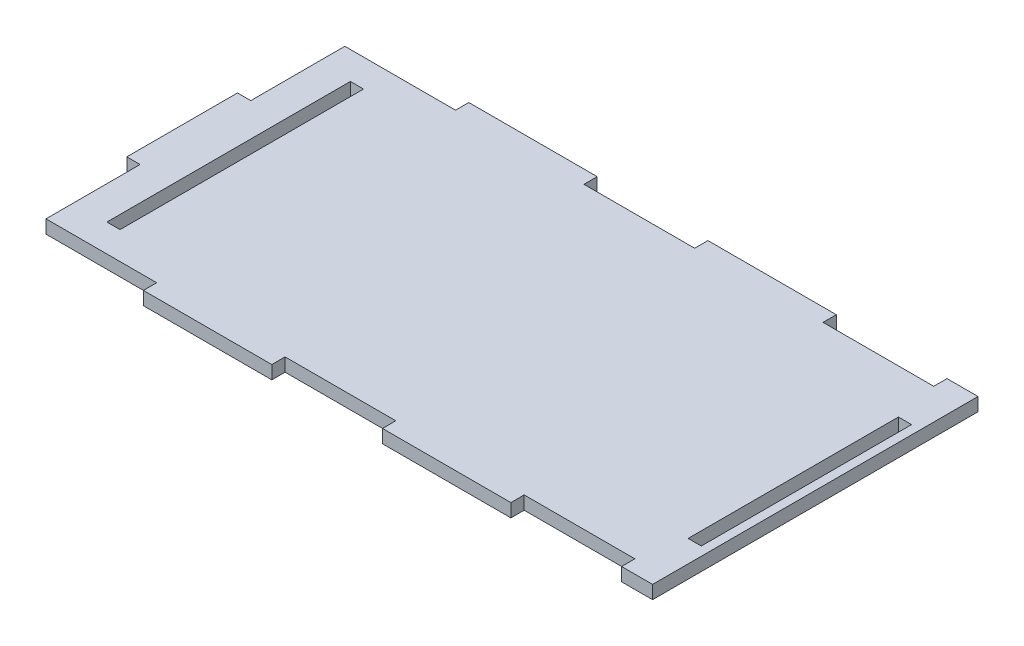
SolidWorks part; units mm, degrees
ref_plane "Alzado" through (0, 0, 0) normal (0, 0, 1) x (1, 0, 0)
ref_plane "Planta" through (0, 0, 0) normal (0, 1, 0) x (1, 0, 0)
ref_plane "Vista lateral" through (0, 0, 0) normal (1, 0, 0) x (0, 0, -1)
sketch "Croquis1" plane through (0, 0, 0) normal (0, 1, 0) x (1, 0, 0)
  line L0 (-139, 0) -> (0, 0) construction
  line L1 (-133, 67.5) -> (133, 67.5)
  line L2 (-133, 67.5) -> (-133, -67.5)
  line L3 (-133, -67.5) -> (133, -67.5)
  line L4 (133, 67.5) -> (133, -67.5)
  line L5 (-133, 67.5) -> (133, -67.5) construction
  line L6 (-133, -67.5) -> (133, 67.5) construction
  line L7 (-83, 67.5) -> (-25, 67.5)
  line L8 (-139, 25) -> (-139, -25) construction
  line L11 (25, 67.5) -> (72.5, 67.5)
  line L24 (-133, -25) -> (-133, 25)
  point P0 (0, 0)
extrude "Saliente-Extruir1" add sketch "Croquis1" along normal blind 6
sketch "Croquis2" plane through (0, 6, 0) normal (0, 1, 0) x (1, 0, 0)
  line L0 (-83, 67.5) -> (-83, 73.5) construction
  line L1 (-83, 67.5) -> (-25, 67.5)
  line L2 (-83, 67.5) -> (-83, 73.5)
  line L3 (-83, 73.5) -> (-25, 73.5)
  line L4 (-25, 67.5) -> (-25, 73.5)
  line L5 (-133, 67.5) -> (133, 67.5) construction
  line L6 (25, 67.5) -> (25, 73.5) construction
  line L7 (25, 67.5) -> (83, 67.5)
  line L8 (25, 67.5) -> (25, 73.5)
  line L9 (25, 73.5) -> (83, 73.5)
  line L10 (83, 67.5) -> (83, 73.5)
  line L11 (-133, -67.5) -> (133, -67.5) construction
  line L12 (-83, -67.5) -> (-25, -67.5)
  line L13 (-83, -67.5) -> (-83, -73.5)
  line L14 (-83, -73.5) -> (-25, -73.5)
  line L15 (-25, -67.5) -> (-25, -73.5)
  line L16 (-83, -73.5) -> (-83, -67.5) construction
  line L17 (25, -73.5) -> (25, -67.5) construction
  line L18 (25, -67.5) -> (83, -67.5)
  line L19 (25, -67.5) -> (25, -73.5)
  line L20 (25, -73.5) -> (83, -73.5)
  line L21 (83, -67.5) -> (83, -73.5)
extrude "Saliente-Extruir2" add sketch "Croquis2" against normal blind 6
sketch "Croquis3" plane through (0, 6, 0) normal (0, 1, 0) x (1, 0, 0)
  line L0 (-139, 0) -> (0, 0) construction
  line L1 (-133, 25) -> (-139, 25)
  line L2 (-133, 25) -> (-133, -25)
  line L3 (-133, -25) -> (-139, -25)
  line L4 (-139, 25) -> (-139, -25)
  line L5 (-133, 67.5) -> (-133, -67.5) construction
  line L6 (-133, 67.5) -> (-83, 67.5) construction
  dimension "D1" = 6
extrude "Saliente-Extruir3" add sketch "Croquis3" against normal blind 6
sketch "Croquis4" plane through (0, 6, 0) normal (0, 1, 0) x (1, 0, 0)
  line L0 (-115.025, 0) -> (-139, 0) construction
  line L1 (-118, 60) -> (-112.05, 60)
  line L2 (-118, 60) -> (-118, -60)
  line L3 (-118, -60) -> (-112.05, -60)
  line L4 (-112.05, 60) -> (-112.05, -60)
  line L5 (-118, 60) -> (-112.05, -60) construction
  line L6 (-118, -60) -> (-112.05, 60) construction
  line L7 (-139, 25) -> (-139, -25) construction
  line L8 (-133, 67.5) -> (-133, 25) construction
  point P0 (-115.025, 0)
  dimension "D1" = 15
  dimension "D2" = 5.95
  dimension "D3" = 120
extrude "Cortar-Extruir1" [suppressed] cut sketch "Croquis4" against normal through all contours L2 L3 L4 L1
sketch "Croquis5" plane through (0, 6, 0) normal (0, 1, 0) x (1, 0, 0)
  line L0 (-118, 0) -> (-112.05, 0) construction
  line L1 (-118, 60) -> (-118, -60) construction
  line L2 (-112.05, 60) -> (-112.05, -60) construction
  line L3 (-115.025, 60) -> (-115.025, -60) construction
  line L4 (-118, 60) -> (-112.05, 60) construction
  line L5 (-118, -60) -> (-112.05, -60) construction
  line L7 (-118, 55) -> (-112.05, 55)
  line L8 (-118, 55) -> (-118, -55)
  line L9 (-118, -55) -> (-112.05, -55)
  line L10 (-112.05, 55) -> (-112.05, -55)
  line L11 (-118, 55) -> (-112.05, -55) construction
  line L12 (-118, -55) -> (-112.05, 55) construction
  point P12 (-115.025, 0)
  dimension "D1" = 5
extrude "Cortar-Extruir2" cut sketch "Croquis5" against normal through all
sketch "Croquis6" plane through (133, 0, 0) normal (1, 0, 0) x (0, 0, -1)
  line L3 (-73.5, 6) -> (73.5, 6)
  line L4 (-73.5, 6) -> (-73.5, 0)
  line L5 (-73.5, 0) -> (73.5, 0)
  line L6 (73.5, 6) -> (73.5, 0)
extrude "Saliente-Extruir4" add sketch "Croquis6" along normal blind 14
sketch "Croquis7" plane through (0, 6, 0) normal (0, 1, 0) x (1, 0, 0)
  line L0 (147, 0) -> (140.025, 0) construction
  line L1 (147, 73.5) -> (147, -73.5) construction
  line L3 (137.05, -47.5) -> (143, -47.5)
  line L4 (137.05, -47.5) -> (137.05, 47.5)
  line L5 (137.05, 47.5) -> (143, 47.5)
  line L6 (143, -47.5) -> (143, 47.5)
  line L7 (137.05, -47.5) -> (143, 47.5) construction
  line L8 (137.05, 47.5) -> (143, -47.5) construction
  line L9 (83, 67.5) -> (133, 67.5) construction
  dimension "D1" = 5.95
  dimension "D2" = 4
  dimension "D3" = 20
extrude "Cortar-Extruir3" cut sketch "Croquis7" against normal through all
sketch "Croquis8" [suppressed] plane through (0, 6, 0) normal (0, 1, 0) x (1, 0, 0)
  line L0 (133, 0) -> (137.05, 0) construction
  line L1 (133, -73.5) -> (147, -73.5)
  line L2 (133, -73.5) -> (133, 73.5)
  line L3 (133, 73.5) -> (147, 73.5)
  line L4 (147, -73.5) -> (147, 73.5)
  line L5 (137.05, 67.5) -> (143, 67.5)
  line L6 (137.05, 67.5) -> (137.05, -67.5)
  line L7 (137.05, -67.5) -> (143, -67.5)
  line L8 (143, 67.5) -> (143, -67.5)
  line L9 (137.05, 0) -> (143, 0) construction
  line L10 (143, 0) -> (147, 0) construction
  line L11 (83, 73.5) -> (25, 73.5) construction
  line L12 (133, -73.5) -> (83, -73.5) construction
  line L13 (147, 73.5) -> (147, -73.5) construction
  line L14 (143, -47.5) -> (143, 47.5) construction
  line L15 (133, 67.5) -> (133, -67.5) construction
  line L16 (137.05, 47.5) -> (137.05, -47.5) construction
  line L17 (83, 67.5) -> (133, 67.5) construction
  line L18 (83, -67.5) -> (133, -67.5) construction
extrude "Saliente-Extruir5" [suppressed] add sketch "Croquis8" against normal blind 6
